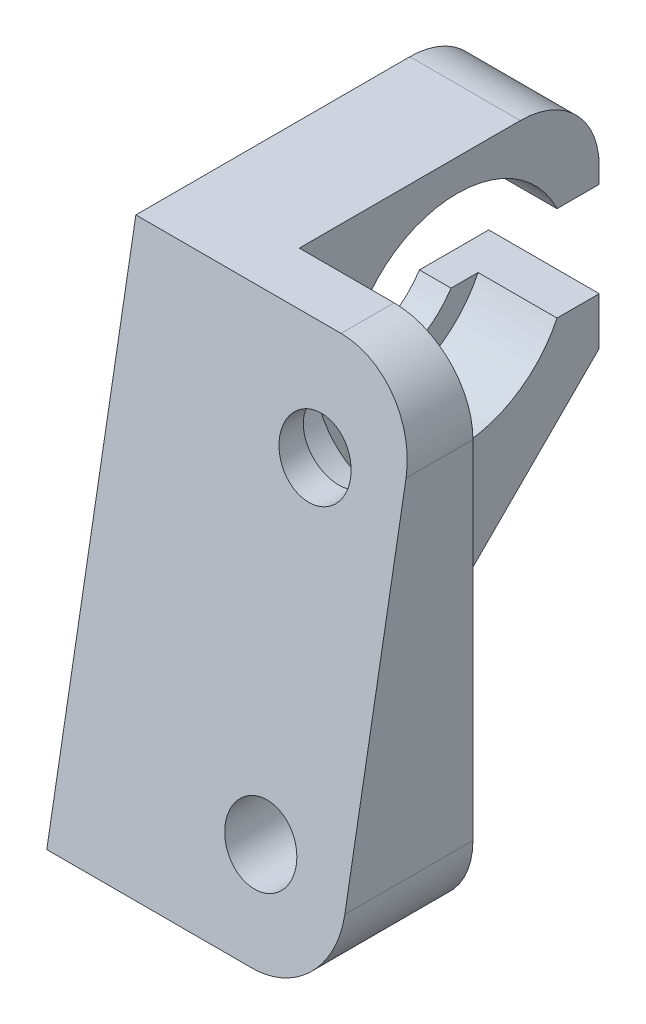
SolidWorks part; units mm, degrees
material "3.1325 (EN-AW 2017A)"
ref_plane "Plan de face" through (0, 0, 0) normal (0, 0, 1) x (1, 0, 0)
ref_plane "Plan de dessus" through (0, 0, 0) normal (0, 1, 0) x (1, 0, 0)
ref_plane "Plan de droite" through (0, 0, 0) normal (1, 0, 0) x (0, 0, -1)
sketch "Esquisse1" plane through (0, 0, 0) normal (1, 0, 0) x (0, 0, -1)
  line L0 (0, 0) -> (5.6425, 32)
  line L1 (5.6425, 32) -> (28, 32)
  line L2 (28, 32) -> (28, 0)
  line L3 (28, 0) -> (0, 0)
  line L4 (0, 0) -> (0, 33.4935) construction
  dimension "D1" = 10
  dimension "D2" = 28
  dimension "D3" = 32
extrude "Boss.-Extru.1" add sketch "Esquisse1" along normal blind 18
sketch "Esquisse2" plane through (0, 32, 0) normal (0, 1, 0) x (1, 0, 0)
  line L0 (18, 28) -> (0, 28) construction
  line L1 (7, 28) -> (18, 28)
  line L2 (7, 28) -> (7, 9)
  line L3 (7, 9) -> (18, 9)
  line L4 (18, 28) -> (18, 9)
  line L5 (18, 28) -> (18, 5.6425) construction
  line L6 (0, 28) -> (0, 5.6425) construction
  dimension "D1" = 7
  dimension "D2" = 9
extrude "Enlèv. mat.-Extru.1" cut sketch "Esquisse2" against normal through all
hole_wizard "Chambrage pour vis à tête hexagonale M41" positions "Esquisse3" profile "Esquisse4" counterbore size "M4" standard "ISO" end condition through all
sketch "Esquisse3" plane through (0, 0, -9) normal (0, 0, -1) x (-1, 0, 0)
  line L0 (-7, 0) -> (-18, 0) construction
  line L1 (-18, 0) -> (-18, 32) construction
  point P0 (-12.5, 6)
  dimension "D1" = 6
  dimension "D2" = 5.5
sketch "Esquisse4" plane through (12.5, 6, -9) normal (1, 0, 0) x (0, 1, 0)
  line L0 (0, 0) -> (0, 9)
  line L1 (0, 9) -> (2.25, 9)
  line L3 (2.25, 9) -> (2.25, 4.4)
  line L4 (2.25, 4.4) -> (4, 4.4)
  line L5 (4, 4.4) -> (4, 0)
  line L7 (4, 0) -> (0, 0)
  line L11 (0, -6.35) -> (0, 107.95) construction
  dimension "Diamètre du perçage jusqu'au prochain" = 4.5
  dimension "Profondeur du perçage jusqu'au prochain" = 9
  dimension "Diamètre du chambrage" = 8
  dimension "Profondeur du chambrage" = 4.4
hole_wizard "Chambrage pour vis à tête hexagonale M44" positions "Esquisse7" profile "Esquisse8" counterbore size "M4" standard "ISO" end condition through all
sketch "Esquisse7" plane through (0, 0, -9) normal (0, 0, -1) x (-1, 0, 0)
  line L0 (-7, 0) -> (-18, 0) construction
  line L1 (-18, 0) -> (-18, 32) construction
  point P0 (-12.5, 25.5)
  dimension "D1" = 25.5
  dimension "D2" = 5.5
sketch "Esquisse8" plane through (12.5, 25.5, -9) normal (1, 0, 0) x (0, 1, 0)
  line L0 (0, 0) -> (0, 9)
  line L1 (0, 9) -> (2.25, 9)
  line L3 (2.25, 9) -> (2.25, 3)
  line L4 (2.25, 3) -> (4.5, 3)
  line L5 (4.5, 3) -> (4.5, 0)
  line L7 (4.5, 0) -> (0, 0)
  line L11 (0, -6.35) -> (0, 107.95) construction
  dimension "Diamètre du perçage jusqu'au prochain" = 4.5
  dimension "Profondeur du perçage jusqu'au prochain" = 9
  dimension "Diamètre du chambrage" = 9
  dimension "Profondeur du chambrage" = 3
sketch "Esquisse9" plane through (7, 0, 0) normal (1, 0, 0) x (0, 0, -1)
  line L0 (0, 0) -> (9, 0) construction
  line L2 (9, 0) -> (9, 32) construction
  circle A0 centre (19, 23) radius 5.5
  dimension "D1" = 11
  dimension "D2" = 23
  dimension "D3" = 10
extrude "Enlèv. mat.-Extru.2" cut sketch "Esquisse9" against normal through all
sketch "Esquisse10" plane through (7, 0, 0) normal (1, 0, 0) x (0, 0, -1)
  circle A0 centre (19, 23) radius 7
  dimension "D1" = 14
extrude "Enlèv. mat.-Extru.3" cut sketch "Esquisse10" against normal blind 5
sketch "Esquisse11" plane through (7, 0, 0) normal (1, 0, 0) x (0, 0, -1)
  line L0 (28, 0) -> (28, 32) construction
  line L1 (19, 26) -> (28, 26)
  line L2 (19, 26) -> (19, 20)
  line L3 (19, 20) -> (28, 20)
  line L4 (28, 26) -> (28, 20)
  circle A0 centre (19, 23) radius 5.5 construction
  point P4 (19, 23)
  point P7 (24, 27)
  dimension "D1" = 6
extrude "Enlèv. mat.-Extru.4" cut sketch "Esquisse11" against normal through all
chamfer "Chanfrein1" distance 17 angle 45 1 edges at (3.5, 0, -28)
fillet "Congé1" radius 5 1 edges at (3.5, 32, -28)
fillet "Congé2" radius 5 2 edges at (18, 0, -4.5) (18, 32, -7.3212)
